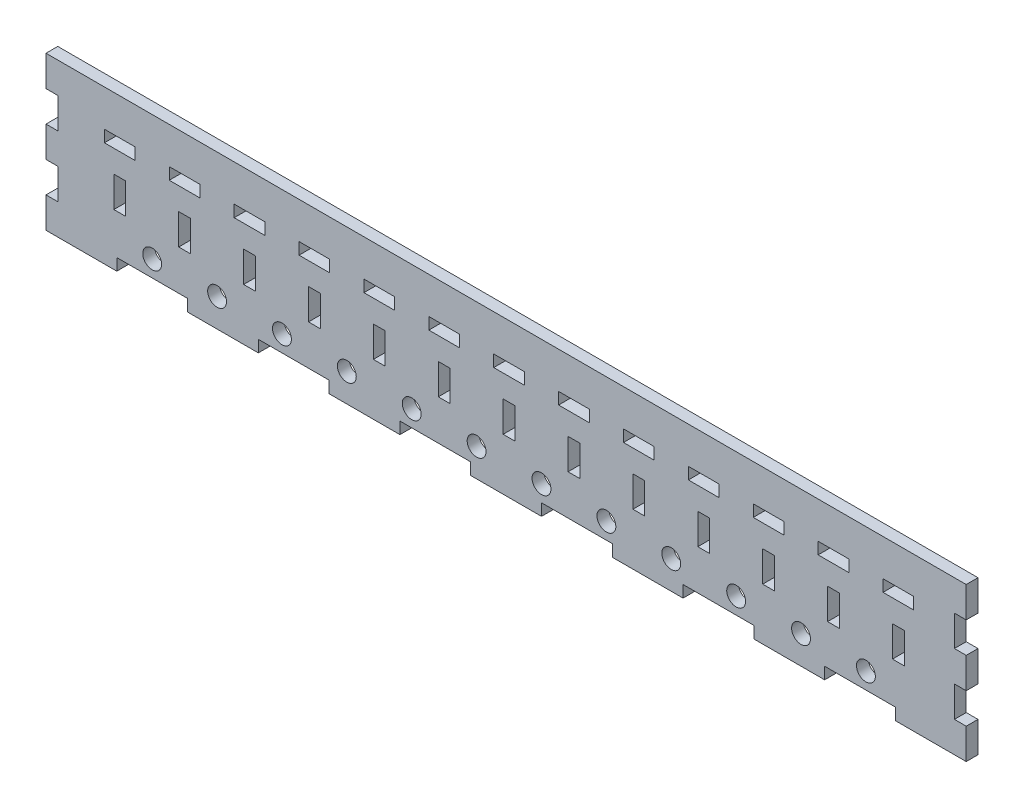
SolidWorks part; units mm, degrees
ref_plane "Plan de face" through (0, 0, 0) normal (0, 0, 1) x (1, 0, 0)
ref_plane "Plan de dessus" through (0, 0, 0) normal (0, 1, 0) x (1, 0, 0)
ref_plane "Plan de droite" through (0, 0, 0) normal (1, 0, 0) x (0, 0, -1)
sketch "Esquisse1" plane through (0, 0, 0) normal (0, 0, 1) x (1, 0, 0)
  line L1 (0, 0) -> (390, 0)
  line L2 (0, 0) -> (0, -65)
  line L3 (0, -65) -> (390, -65)
  line L4 (390, 0) -> (390, -65)
  dimension "D1" = 390
  dimension "D2" = 65
extrude "Boss.-Extru.1" add sketch "Esquisse1" along normal blind 5
sketch "Esquisse2" plane through (0, 0, 5) normal (0, 0, 1) x (1, 0, 0)
  line L0 (0, -65) -> (390, -65) construction
  line L1 (30, -65) -> (60, -65)
  line L2 (30, -65) -> (30, -60)
  line L3 (30, -60) -> (60, -60)
  line L4 (60, -65) -> (60, -60)
  line L5 (0, 0) -> (390, 0) construction
  line L6 (0, 0) -> (0, -65) construction
  dimension "D1" = 390
  dimension "D2" = 30
  dimension "D3" = 30
  dimension "D4" = 5
extrude "Enlèv. mat.-Extru.1" cut sketch "Esquisse2" against normal blind 5
pattern_linear "Répétition linéaire1" count 6 spacing 60 along (1, 0, 0) of "Enlèv. mat.-Extru.1"
sketch "Esquisse3" plane through (0, 0, 5) normal (0, 0, 1) x (1, 0, 0)
  line L0 (0, 0) -> (0, -65) construction
  line L1 (0, -52) -> (5, -52)
  line L2 (0, -52) -> (0, -39)
  line L3 (0, -39) -> (5, -39)
  line L4 (5, -52) -> (5, -39)
  line L5 (0, 0) -> (0, -65) construction
  line L6 (0, -65) -> (30, -65) construction
  dimension "D4" = 5
  dimension "D1" = 65
  dimension "D2" = 13
  dimension "D3" = 13
extrude "Enlèv. mat.-Extru.2" cut sketch "Esquisse3" against normal blind 5
pattern_linear "Répétition linéaire2" count 2 spacing 26 along (0, 1, 0) of "Enlèv. mat.-Extru.2"
ref_plane "Plan1" through (195, 0, 0) normal (-1, 0, 0) x (0, 0, 1)
mirror "Symétrie1" about plane through (195, 0, 0) normal (-1, 0, 0) of "Répétition linéaire2", "Enlèv. mat.-Extru.2"
sketch "Esquisse4" plane through (0, 0, 5) normal (0, 0, 1) x (1, 0, 0)
  line L0 (0, -52) -> (0, -65) construction
  line L1 (60, -65) -> (90, -65) construction
  circle A0 centre (100, -53) radius 4
  dimension "D3" = 8
  dimension "D1" = 100
  dimension "D2" = 12
extrude "Enlèv. mat.-Extru.3" cut sketch "Esquisse4" against normal blind 5
pattern_linear "Répétition linéaire3" count 10 spacing 27.5 along (1, 0, 0) count 3 spacing 27.5 along (-1, 0, 0) of "Enlèv. mat.-Extru.3"
sketch "Esquisse5" plane through (0, 0, 5) normal (0, 0, 1) x (1, 0, 0)
  line L1 (83.75, -30) -> (88.75, -30)
  line L2 (83.75, -30) -> (83.75, -43)
  line L3 (83.75, -43) -> (88.75, -43)
  line L4 (88.75, -30) -> (88.75, -43)
  line L5 (60, -65) -> (90, -65) construction
  line L6 (100, -49) -> (100, -24.8053) construction
  line L11 (120, -60) -> (90, -60) construction
  line L12 (79.75, -15.5) -> (92.75, -15.5)
  line L13 (79.75, -15.5) -> (79.75, -20.5)
  line L14 (79.75, -20.5) -> (92.75, -20.5)
  line L15 (92.75, -15.5) -> (92.75, -20.5)
  line L16 (86.25, -15.5) -> (86.25, -20.5) construction
  line L17 (86.25, -30) -> (86.25, -43) construction
  circle A0 centre (100, -53) radius 4 construction
  point P10 (100, -53)
  dimension "D2" = 13
  dimension "D3" = 5
  dimension "D4" = 35
  dimension "D5" = 39.5
  dimension "D6" = 5
  dimension "D7" = 13
  dimension "D1" = 13.75
extrude "Enlèv. mat.-Extru.4" cut sketch "Esquisse5" against normal blind 5
pattern_linear "Répétition linéaire4" count 3 spacing 27.5 along (-1, 0, 0) count 11 spacing 27.5 along (1, 0, 0) of "Enlèv. mat.-Extru.4"
equation "\"D1@Esquisse1\"=400-10"
equation "\"D2@Esquisse2\"=\"D1@Esquisse2\"/13"
equation "\"D3@Esquisse2\"=\"D1@Esquisse2\"/13"
equation "\"D2@Esquisse3\"=\"D1@Esquisse3\"/5"
equation "\"D3@Esquisse3\"=\"D1@Esquisse3\"/5"
equation "\"D6@Esquisse5\"=\"D3@Esquisse5\""
equation "\"D1@Esquisse5\"=22.5/2+2.5"
